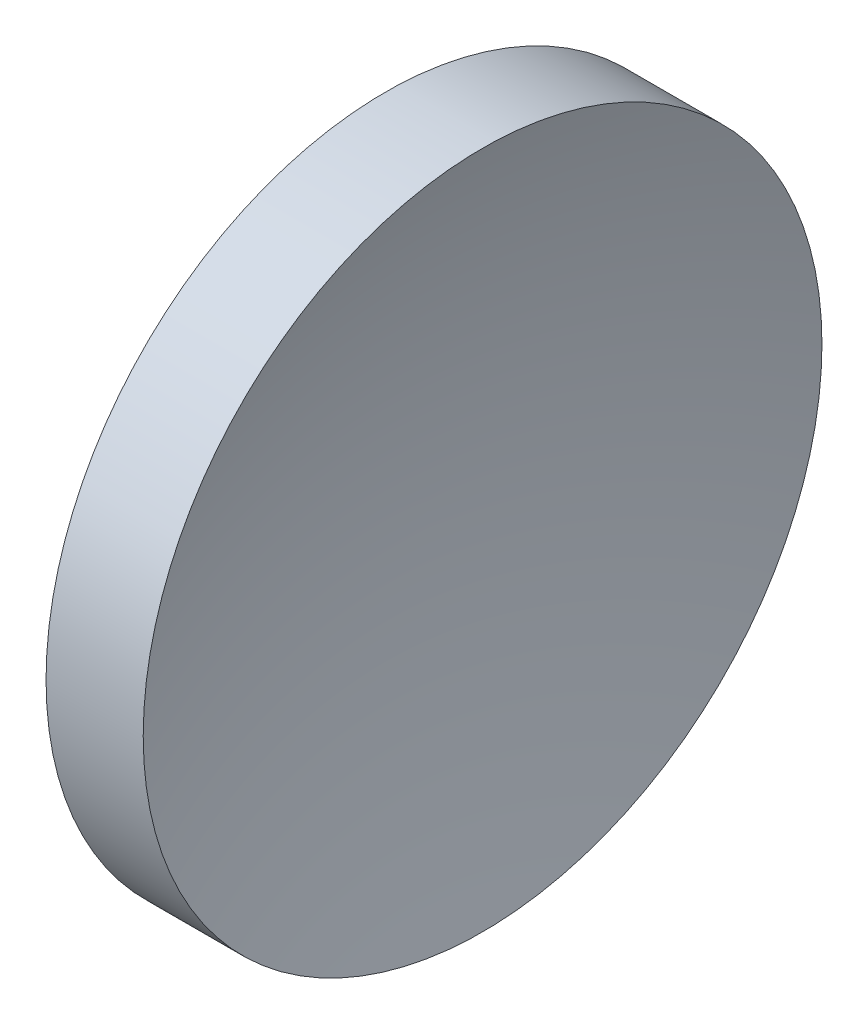
SolidWorks part; units mm, degrees
ref_plane "前视基准面" through (0, 0, 0) normal (0, 0, 1) x (1, 0, 0)
ref_plane "上视基准面" through (0, 0, 0) normal (0, 1, 0) x (1, 0, 0)
ref_plane "右视基准面" through (0, 0, 0) normal (1, 0, 0) x (0, 0, -1)
sketch "草图1" plane through (0, 0, 0) normal (0, 0, 1) x (1, 0, 0)
  line L0 (105.6218, 65.1556) -> (137.1869, 65.1556) construction
  line L1 (113.9119, 65.1556) -> (113.9119, 85.1556)
  line L2 (113.9119, 85.1556) -> (119.6382, 85.1556)
  line L3 (116.4119, 65.1556) -> (113.9119, 65.1556)
  arc A0 (119.6382, 85.1556) -> (116.4119, 65.1556) centre (180.9618, 65.0031) ccw
revolve "旋转1" add sketch "草图1" angle 360 about L0
